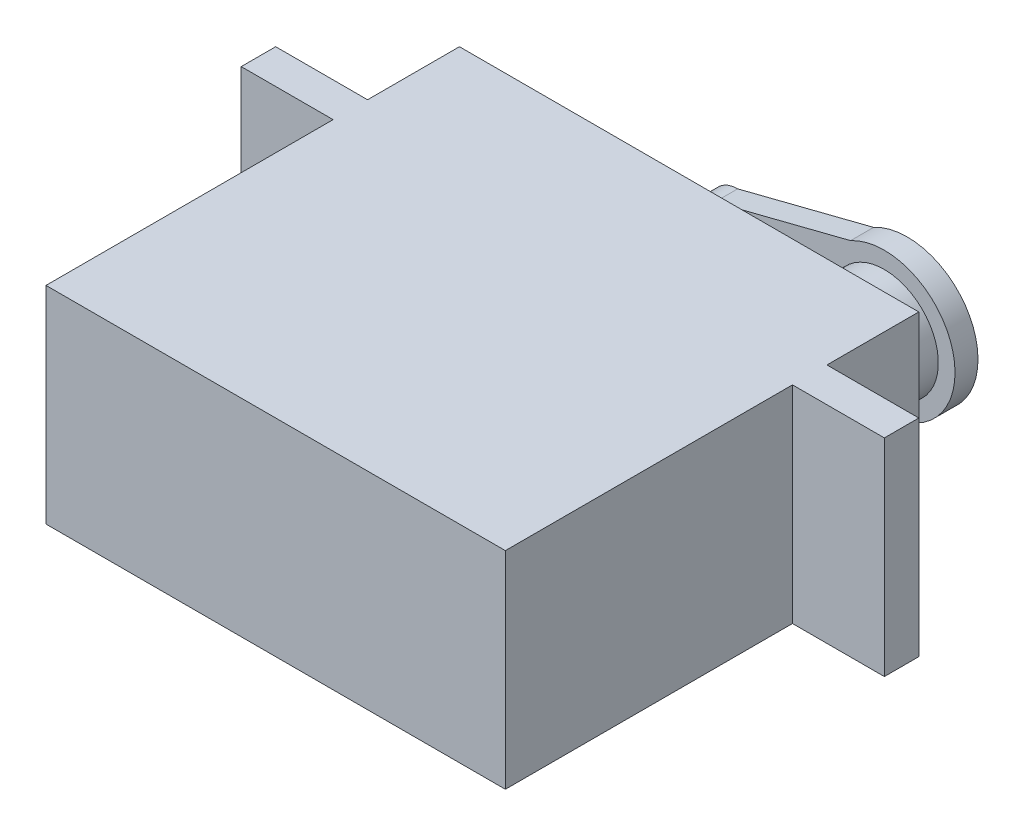
SolidWorks part; units mm, degrees
ref_plane "Спереди" through (0, 0, 0) normal (0, 0, 1) x (1, 0, 0)
ref_plane "Сверху" through (0, 0, 0) normal (0, 1, 0) x (1, 0, 0)
ref_plane "Справа" through (0, 0, 0) normal (1, 0, 0) x (0, 0, -1)
sketch "Эскиз1" plane through (0, 0, 0) normal (0, 0, 1) x (1, 0, 0)
  line L0 (0, 0) -> (0, 18)
  line L1 (0, 18) -> (-56, 18)
  line L2 (-56, 18) -> (-56, 0)
  line L3 (-56, 0) -> (0, 0)
extrude "Бобышка-Вытянуть1" add sketch "Эскиз1" along normal blind 3 contours L1 L2 L3 L0
sketch "Эскиз2" plane through (0, 0, 3) normal (0, 0, 1) x (1, 0, 0)
  line L0 (-56, 18) -> (-28, 18)
  line L1 (0, 18) -> (-56, 18) construction
  line L2 (-28, 18) -> (-48, 18)
  line L3 (-48, 18) -> (-8, 18)
  line L4 (-8, 18) -> (-8, 0)
  line L5 (-56, 0) -> (0, 0) construction
  line L6 (-8, 0) -> (-48, 0)
  line L7 (-48, 0) -> (-48, 18)
  line M2 (0, 18) -> (-56, 18)
  line M4 (-56, 0) -> (0, 0)
extrude "Бобышка-Вытянуть2" add sketch "Эскиз2" along normal blind 25 contours L7 L4 M4 M2
sketch "Эскиз3" plane through (0, 0, 0) normal (0, 0, -1) x (-1, 0, 0)
  line L0 (28, 18) -> (8, 18)
  line L1 (0, 18) -> (56, 18) construction
  line L2 (8, 18) -> (48, 18)
  line L3 (48, 18) -> (48, 0)
  line L4 (48, 0) -> (8, 0)
  line L5 (8, 0) -> (8, 18)
  line M2 (0, 0) -> (56, 0)
  line M4 (56, 18) -> (0, 18)
extrude "Бобышка-Вытянуть3" add sketch "Эскиз3" along normal blind 8 contours L5 L3 M2 M4
sketch "Эскиз4" plane through (0, 0, -8) normal (0, 0, -1) x (-1, 0, 0)
  line L0 (8, 9) -> (17, 9)
  line L1 (8, 0) -> (8, 18) construction
  circle A0 centre (17, 9) radius 4.7
extrude "Бобышка-Вытянуть4" add sketch "Эскиз4" along normal blind 6
sketch "Эскиз5" plane through (0, 0, -14) normal (0, 0, -1) x (-1, 0, 0)
  line L1 (19.9413, 14.4063) -> (31.7703, 11.3968)
  line L3 (31.7703, 6.6032) -> (19.9413, 3.5937)
  arc A0 (19.9413, 14.4063) -> (19.9413, 3.5937) centre (17, 9) ccw
  arc A1 (31.7703, 6.6032) -> (31.7703, 11.3968) centre (31.7703, 9) ccw
extrude "Бобышка-Вытянуть5" add sketch "Эскиз5" along normal blind 2
